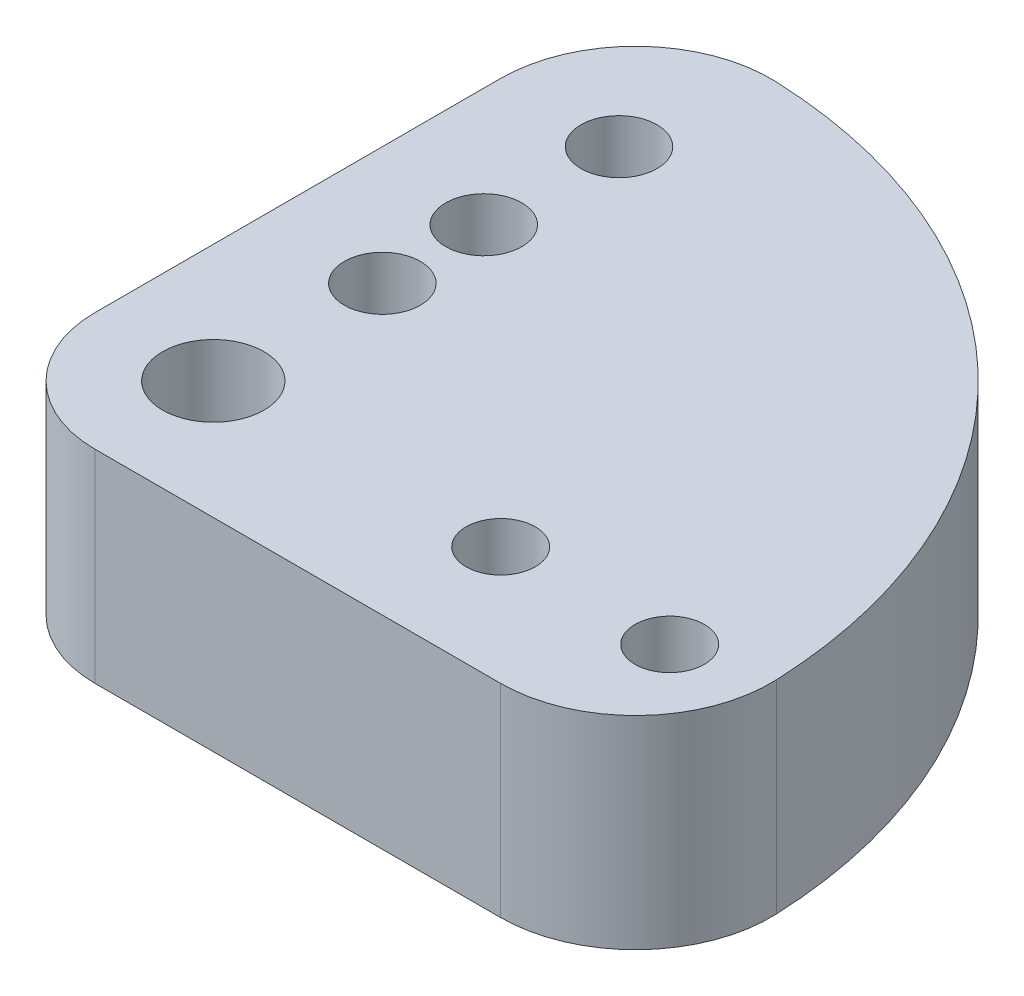
SolidWorks part; units mm, degrees
ref_plane "前视基准面" through (0, 0, 0) normal (0, 0, 1) x (1, 0, 0)
ref_plane "上视基准面" through (0, 0, 0) normal (0, 1, 0) x (1, 0, 0)
ref_plane "右视基准面" through (0, 0, 0) normal (1, 0, 0) x (0, 0, -1)
other "Configuration Table"
sketch "草图1" plane through (0, 0, 0) normal (0, 1, 0) x (1, 0, 0)
  line L0 (0, 0) -> (50000, 0) construction
  line L1 (0, -3.5) -> (15.6125, -3.5)
  line L2 (-3.5, 0) -> (-3.5, 15.6125)
  line L3 (0, 0) -> (0, 20) construction
  line L4 (13.6852, 2.4931) -> (0.2593, 3.4904) construction
  line L5 (-3.5, 0) -> (16, 0) construction
  line L6 (-3.5, 0) -> (-3.5, -10) construction
  line L7 (-3.5, -10) -> (16, -10) construction
  line L8 (16, 0) -> (16, -10) construction
  circle A0 centre (0, 0) radius 16 construction
  circle A1 centre (8.5, 0) radius 1.025
  circle A2 centre (13.5, 0) radius 1.025
  circle A3 centre (6, 0) radius 1.025 construction
  circle A4 centre (0, 0) radius 1.5
  arc A5 (15.6125, -3.5) -> (-3.5, 15.6125) centre (0, 0) ccw
  arc A6 (-3.5, 0) -> (0, -3.5) centre (0, 0) ccw
  circle A7 centre (0, 20) radius 1.125 construction
  circle A8 centre (0, 16) radius 1.125 construction
  circle A9 centre (0, 12) radius 1.125
  circle A10 centre (0, 0) radius 3.5 construction
  circle A11 centre (13.5, 0) radius 2.5 construction
  circle A12 centre (0, 8) radius 1.125
  circle A13 centre (0, 5) radius 1.125
  dimension "D1" = 32
  dimension "D2" = 2.05
  dimension "D6" = 3
  dimension "D9" = 2.25
  dimension "D13" = 7
  dimension "D3" = 8.5
  dimension "D4" = 13.5
  dimension "D5" = 6
  dimension "D8" = 20
  dimension "D10" = 16
  dimension "D11" = 12
  dimension "D12" = 90
  dimension "D14" = 10
  dimension "D15" = 19.5
  dimension "D16" = 8
  dimension "D17" = 5
extrude "凸台-拉伸1" add sketch "草图1" along normal blind 6
sketch "草图2" plane through (0, 6, 0) normal (0, 1, 0) x (1, 0, 0)
  line L0 (2.5, 3.7) -> (2.5, 15.8035)
  line L1 (2.5, 3.7) -> (-3.5, 3.7)
  line L2 (-3.5, 15.6125) -> (-3.5, 0)
  line L3 (0, -3.5) -> (15.6125, -3.5)
  line L4 (-3.5, 15.6125) -> (-3.5, 0)
  line L5 (0, -3.5) -> (15.6125, -3.5)
  circle A0 centre (0, 12) radius 1.125 construction
  circle A1 centre (0, 8) radius 1.125 construction
  arc A2 (15.6125, -3.5) -> (-3.5, 15.6125) centre (0, 0) ccw
  arc A3 (-3.5, 0) -> (0, -3.5) centre (0, 0) ccw
  arc A4 (15.6125, -3.5) -> (-3.5, 15.6125) centre (0, 0) ccw
  arc A5 (-3.5, 0) -> (0, -3.5) centre (0, 0) ccw
  circle A6 centre (0, 5) radius 1.125 construction
  circle A7 centre (0, 12) radius 1.125
  circle A8 centre (0, 8) radius 1.125
  circle A9 centre (0, 5) radius 1.125
  circle M7 centre (0, 8) radius 1.125
  arc M10 (15.6125, -3.5) -> (-3.5, 15.6125) centre (0, 0) ccw
  line M11 (-3.5, 15.6125) -> (-3.5, 0)
  circle M15 centre (0, 12) radius 1.125
  circle M16 centre (0, 5) radius 1.125
  dimension "D2" = 3.7
  dimension "D3" = 6
  dimension "D1" = 0
extrude "凸台-拉伸2" [suppressed] add sketch "草图2" along normal blind 4 contours L1 L0 M10 M11 M15 M16 M7
sketch "草图3" plane through (0, 0, 0) normal (0, -1, 0) x (1, 0, 0)
  circle A0 centre (0, 0) radius 2.5
  dimension "D1" = 5
extrude "切除-拉伸1" cut sketch "草图3" against normal blind 3
fillet "圆角1" radius 4 2 edges at (-3.5, 3, -15.6125) (15.6125, 3, 3.5)
chamfer "倒角1" [suppressed] distance 1 angle 45
